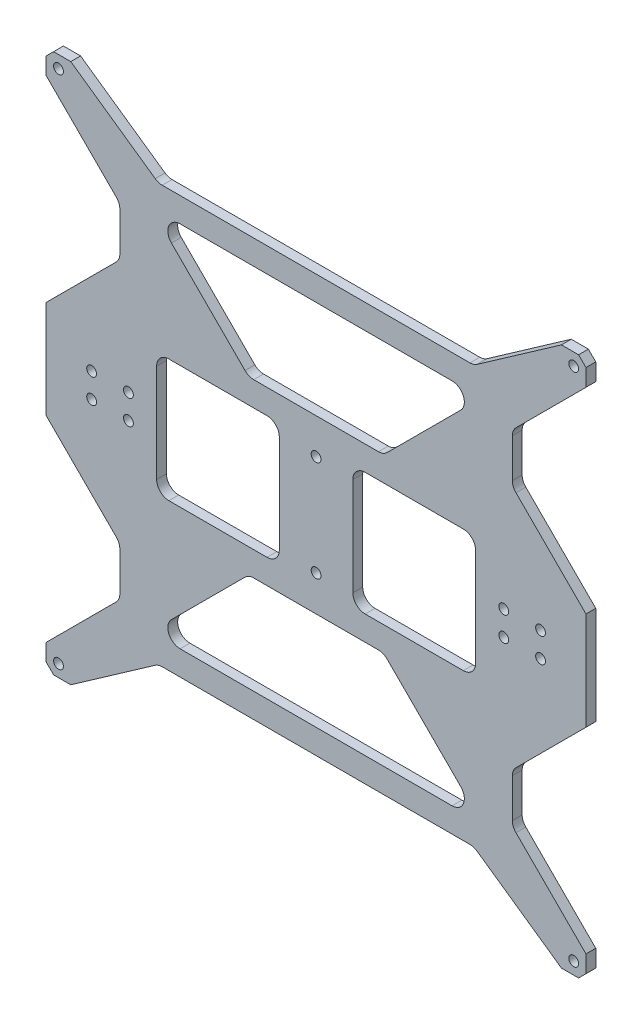
SolidWorks part; units mm, degrees
ref_plane "Plan de face" through (0, 0, 0) normal (0, 0, 1) x (1, 0, 0)
ref_plane "Plan de dessus" through (0, 0, 0) normal (0, 1, 0) x (1, 0, 0)
ref_plane "Plan de droite" through (0, 0, 0) normal (1, 0, 0) x (0, 0, -1)
sketch "Esquisse1" plane through (0, 0, 0) normal (0, 0, 1) x (1, 0, 0)
  line L0 (-105.8752, 88.2292) -> (-105.8752, -131.7708) construction
  line L1 (-131.8752, 88.2292) -> (88.1248, 88.2292)
  line L2 (-131.8752, 88.2292) -> (-131.8752, -131.7708)
  line L3 (-131.8752, -131.7708) -> (88.1248, -131.7708)
  line L4 (88.1248, 88.2292) -> (88.1248, -131.7708)
  line L5 (62.1248, 88.2292) -> (62.1248, -131.7708) construction
  line L6 (-131.8752, -21.7708) -> (88.1248, -21.7708) construction
  line L7 (-21.8752, 88.2292) -> (-21.8752, -131.7708) construction
  circle A0 centre (-126.8752, 83.2292) radius 2
  circle A1 centre (83.1248, 83.2292) radius 2
  circle A2 centre (-126.8752, -126.7708) radius 2
  circle A3 centre (83.1248, -126.7708) radius 2
  circle A4 centre (-113.3752, -16.7708) radius 2
  circle A5 centre (-98.3752, -16.7708) radius 2
  circle A6 centre (-113.3752, -26.7708) radius 2
  circle A7 centre (-98.3752, -26.7708) radius 2
  circle A8 centre (54.6248, -16.7708) radius 2
  circle A9 centre (69.6248, -16.7708) radius 2
  circle A10 centre (54.6248, -26.7708) radius 2
  circle A11 centre (69.6248, -26.7708) radius 2
  circle A12 centre (-21.8752, -1.2708) radius 2
  circle A13 centre (-21.8752, -42.2708) radius 2
  dimension "D2" = 4
  dimension "D3" = 4
  dimension "D4" = 4
  dimension "D5" = 4
  dimension "D14" = 4
  dimension "D15" = 4
  dimension "D16" = 4
  dimension "D17" = 4
  dimension "D22" = 4
  dimension "D23" = 4
  dimension "D24" = 4
  dimension "D25" = 4
  dimension "D33" = 4
  dimension "D34" = 4
  dimension "D1" = 220
  dimension "220" = 220
  dimension "D6" = 5
  dimension "D7" = 5
  dimension "D8" = 5
  dimension "D9" = 5
  dimension "D10" = 5
  dimension "D11" = 5
  dimension "D12" = 5
  dimension "D13" = 5
  dimension "D18" = 10
  dimension "D19" = 10
  dimension "D20" = 10
  dimension "D21" = 10
  dimension "D26" = 5
  dimension "D27" = 15
  dimension "D28" = 15
  dimension "D29" = 7.5
  dimension "D30" = 7.5
  dimension "D31" = 26
  dimension "D32" = 26
  dimension "D35" = 41
  dimension "D36" = 20.5
extrude "Boss.-Extru.1" add sketch "Esquisse1" along normal blind 4
sketch "Esquisse2" plane through (0, 0, 4) normal (0, 0, 1) x (1, 0, 0)
  line L0 (-89.3752, 53.2292) -> (45.6248, 53.2292)
  line L1 (-49.3752, 13.2292) -> (5.6248, 13.2292)
  line L2 (-89.3752, 53.2292) -> (-49.3752, 13.2292)
  line L3 (5.6248, 13.2292) -> (45.6248, 53.2292)
  line L4 (-89.3752, -96.7708) -> (45.6248, -96.7708)
  line L5 (45.6248, -96.7708) -> (5.6248, -56.7708)
  line L6 (5.6248, -56.7708) -> (-49.3752, -56.7708)
  line L7 (-49.3752, -56.7708) -> (-89.3752, -96.7708)
  line L8 (-21.8752, 88.2292) -> (-21.8752, -131.7708) construction
  line L9 (88.1248, 88.2292) -> (-131.8752, 88.2292) construction
  line L10 (-131.8752, -131.7708) -> (88.1248, -131.7708) construction
  line L11 (88.1248, -41.7708) -> (58.1248, -71.7708)
  line L12 (88.1248, -131.7708) -> (88.1248, 88.2292) construction
  line L13 (58.1248, -71.7708) -> (58.1248, -91.7708)
  line L14 (58.1248, -91.7708) -> (88.1248, -121.7708)
  line L15 (88.1248, -41.7708) -> (88.1248, -121.7708)
  line L16 (88.1248, 78.2292) -> (88.1248, -1.7708)
  line L17 (88.1248, -1.7708) -> (58.1248, 28.2292)
  line L18 (58.1248, 28.2292) -> (58.1248, 48.2292)
  line L19 (58.1248, 48.2292) -> (88.1248, 78.2292)
  line L20 (-131.8752, 78.2292) -> (-131.8752, -1.7708)
  line L21 (-131.8752, 88.2292) -> (-131.8752, -131.7708) construction
  line L22 (-131.8752, -1.7708) -> (-101.8752, 28.2292)
  line L23 (-101.8752, 28.2292) -> (-101.8752, 48.2292)
  line L24 (-101.8752, 48.2292) -> (-131.8752, 78.2292)
  line L25 (-131.8752, -41.7708) -> (-101.8752, -71.7708)
  line L26 (-101.8752, -71.7708) -> (-101.8752, -91.7708)
  line L27 (-101.8752, -91.7708) -> (-131.8752, -121.7708)
  line L28 (-131.8752, -121.7708) -> (-131.8752, -41.7708)
  line L29 (-131.8752, -21.7708) -> (88.1248, -21.7708) construction
  line L30 (18.1248, 3.2292) -> (18.1248, -46.7708) construction
  line L31 (-6.8752, 3.2292) -> (43.1248, 3.2292)
  line L32 (-6.8752, 3.2292) -> (-6.8752, -46.7708)
  line L33 (-6.8752, -46.7708) -> (43.1248, -46.7708)
  line L34 (43.1248, 3.2292) -> (43.1248, -46.7708)
  line L35 (-61.8752, 3.2292) -> (-61.8752, -46.7708) construction
  line L36 (-86.8752, 3.2292) -> (-36.8752, 3.2292)
  line L37 (-86.8752, 3.2292) -> (-86.8752, -46.7708)
  line L38 (-86.8752, -46.7708) -> (-36.8752, -46.7708)
  line L39 (-36.8752, 3.2292) -> (-36.8752, -46.7708)
  line L46 (-121.8752, -131.7708) -> (-86.1715, -106.7708)
  line L47 (-86.1715, -106.7708) -> (42.4211, -106.7708)
  line L48 (42.4211, -106.7708) -> (78.1248, -131.7708)
  line L49 (78.1248, -131.7708) -> (-121.8752, -131.7708)
  line L50 (-121.8752, 88.2292) -> (-86.1715, 63.2292)
  line L51 (-86.1715, 63.2292) -> (42.4211, 63.2292)
  line L52 (42.4211, 63.2292) -> (78.1248, 88.2292)
  line L53 (78.1248, 88.2292) -> (-121.8752, 88.2292)
  dimension "D33" = 50
  dimension "D1" = 45
  dimension "D2" = 45
  dimension "D3" = 45
  dimension "D4" = 45
  dimension "D5" = 35
  dimension "D6" = 55
  dimension "D7" = 55
  dimension "D8" = 40
  dimension "D9" = 27.5
  dimension "D10" = 27.5
  dimension "D11" = 10
  dimension "D12" = 70
  dimension "D13" = 45
  dimension "D14" = 45
  dimension "D15" = 30
  dimension "D16" = 10
  dimension "D17" = 45
  dimension "D18" = 45
  dimension "D19" = 30
  dimension "D20" = 10
  dimension "D21" = 80
  dimension "D22" = 80
  dimension "D23" = 80
  dimension "D24" = 45
  dimension "D25" = 45
  dimension "D26" = 30
  dimension "D27" = 10
  dimension "D28" = 30
  dimension "D29" = 10
  dimension "D30" = 80
  dimension "D31" = 45
  dimension "D32" = 45
  dimension "D34" = 50
  dimension "D35" = 40
  dimension "D36" = 50
  dimension "D37" = 50
  dimension "D38" = 40
  dimension "D39" = 25
  dimension "D40" = 25
  dimension "D48" = 10
  dimension "D49" = 10
  dimension "D50" = 10
  dimension "D51" = 35
  dimension "D52" = 35
  dimension "D53" = 10
  dimension "D54" = 10
  dimension "D55" = 35
  dimension "D56" = 35
  dimension "D57" = 40
extrude "Enlèv. mat.-Extru.1" cut sketch "Esquisse2" against normal through all
fillet "Congé1" radius 5 4 edges at (-89.3752, -96.7708, 2) (45.6248, -96.7708, 2) (45.6248, 53.2292, 2) (-89.3752, 53.2292, 2)
chamfer "Chanfrein1" distance 3 angle 45 4 edges at (88.1248, -131.7708, 2) (88.1248, 88.2292, 2) (-131.8752, -131.7708, 2) (-131.8752, 88.2292, 2)
fillet "Congé2" radius 5 24 edges at (42.4211, -106.7708, 2) (-86.1715, -106.7708, 2) (5.6248, -56.7708, 2) (-49.3752, -56.7708, 2) (58.1248, -91.7708, 2) (58.1248, -71.7708, 2) (-101.8752, -91.7708, 2) (-101.8752, -71.7708, 2) (-101.8752, 28.2292, 2) (-101.8752, 48.2292, 2) (58.1248, 28.2292, 2) (58.1248, 48.2292, 2) (5.6248, 13.2292, 2) (-49.3752, 13.2292, 2) (42.4211, 63.2292, 2) (-86.1715, 63.2292, 2) (-6.8752, -46.7708, 2) (-86.8752, -46.7708, 2) (-36.8752, -46.7708, 2) (43.1248, -46.7708, 2) (43.1248, 3.2292, 2) (-36.8752, 3.2292, 2) (-6.8752, 3.2292, 2) (-86.8752, 3.2292, 2)
